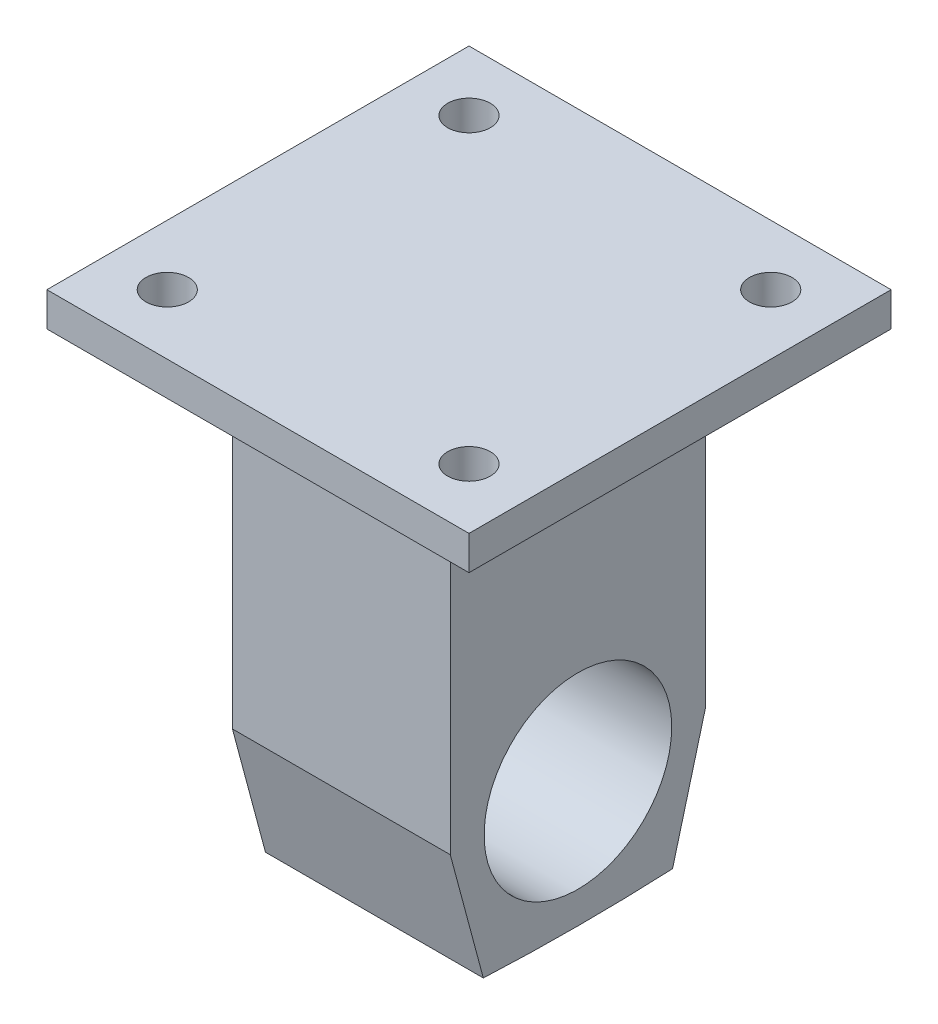
SolidWorks part; units mm, degrees
material "ABS"
ref_plane "Front Plane" through (0, 0, 0) normal (0, 0, 1) x (1, 0, 0)
ref_plane "Top Plane" through (0, 0, 0) normal (0, 1, 0) x (1, 0, 0)
ref_plane "Right Plane" through (0, 0, 0) normal (1, 0, 0) x (0, 0, -1)
sketch "Sketch1" plane through (0, 0, 0) normal (0, 1, 0) x (1, 0, 0)
  line L1 (-16.256, -19.05) -> (16.256, -19.05)
  line L2 (-16.256, -19.05) -> (-16.256, 19.05)
  line L3 (-16.256, 19.05) -> (16.256, 19.05)
  line L4 (16.256, -19.05) -> (16.256, 19.05)
  line L5 (-16.256, -19.05) -> (16.256, 19.05) construction
  line L6 (-16.256, 19.05) -> (16.256, -19.05) construction
  point P0 (0, 0)
extrude "Boss-Extrude1" add sketch "Sketch1" along normal blind 50.292
sketch "Sketch2" plane through (16.256, 0, 0) normal (1, 0, 0) x (0, 0, -1)
  line L0 (-19.05, 0) -> (-14.1195, -18.4009)
  line L1 (19.05, 0) -> (14.1195, -18.4009)
  line L2 (-19.05, 0) -> (19.05, 0)
  line L3 (-19.05, 0) -> (19.05, 0) construction
  arc A1 (14.1195, -18.4009) -> (-14.1195, -18.4009) centre (0, 281.2546) cw
  dimension "D1" = 19.05
  dimension "D2" = 19.05
  dimension "D3" = 75
  dimension "D4" = 75
extrude "Boss-Extrude2" add sketch "Sketch2" against normal up to vertex (32.512 mm away) contours L0 A1 L1 L2 up to point (-16.256, 0, -19.05)
sketch "Sketch3" plane through (16.256, 0, 0) normal (1, 0, 0) x (0, 0, -1)
  circle A0 centre (0, 0) radius 14
extrude "Cut-Extrude1" cut sketch "Sketch3" against normal blind 127 contours A0
sketch "Sketch4" plane through (0, 50.292, 0) normal (0, 1, 0) x (1, 0, 0)
  line L0 (34.2946, -34.2946) -> (-34.2946, 34.2946) construction
  line L5 (37.2621, 37.2621) -> (-37.2621, -37.2621) construction
  line L6 (-31.496, 31.496) -> (31.496, 31.496)
  line L11 (31.496, 31.496) -> (31.496, -31.496)
  line L12 (31.496, -31.496) -> (-31.496, -31.496)
  line L13 (-31.496, -31.496) -> (-31.496, 31.496)
  line L14 (31.496, 31.496) -> (-31.496, -31.496) construction
  line L15 (31.496, -31.496) -> (-31.496, 31.496) construction
  point P1 (0, 0)
  point P4 (0, 0)
  point P11 (0, 0)
  dimension "D1" = 62.992
  dimension "D2" = 62.992
  dimension "D3" = 0
  dimension "D4" = 0
extrude "Boss-Extrude3" add sketch "Sketch4" along normal blind 5.08
sketch "Sketch5" plane through (0, 55.372, 0) normal (0, 1, 0) x (1, 0, 0)
  line L2 (-22.5157, 22.5157) -> (-31.496, 31.496) construction
  line L3 (22.5157, 22.5157) -> (31.496, 31.496) construction
  line L4 (22.5157, -22.5157) -> (31.496, -31.496) construction
  line L5 (-22.5157, -22.5157) -> (-31.496, -31.496) construction
  line L6 (-31.496, -31.496) -> (31.496, -31.496) construction
  line L7 (-31.496, 31.496) -> (-31.496, -31.496) construction
  line L8 (31.496, -31.496) -> (31.496, 31.496) construction
  circle A0 centre (-22.5157, 22.5157) radius 3.175
  circle A1 centre (22.5157, 22.5157) radius 3.175
  circle A2 centre (-22.5157, -22.5157) radius 3.175
  circle A3 centre (22.5157, -22.5157) radius 3.175
  dimension "D2" = 6.35
  dimension "D4" = 6.35
  dimension "D11" = 6.35
  dimension "D12" = 6.35
  dimension "D1" = 12.7
  dimension "D3" = 45
  dimension "D5" = 12.7
  dimension "D6" = 45
  dimension "D7" = 12.7
  dimension "D8" = 45
  dimension "D9" = 12.7
  dimension "D10" = 45
extrude "Cut-Extrude2" cut sketch "Sketch5" against normal through all
